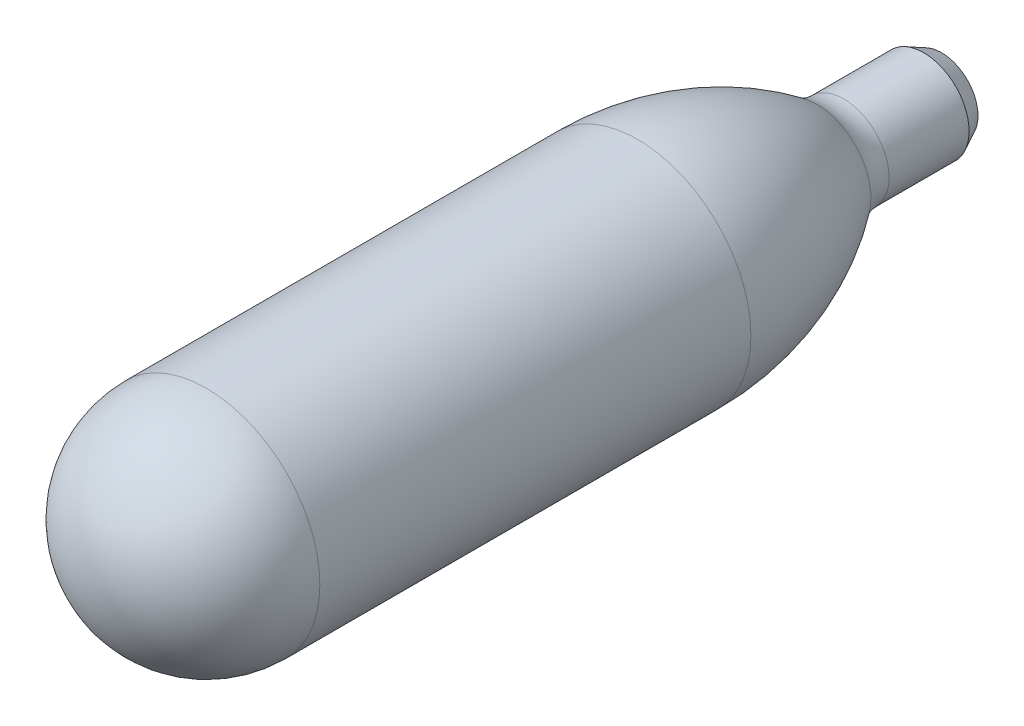
SolidWorks part; units mm, degrees
material "AISI 304"
ref_plane "Front Plane" through (0, 0, 0) normal (0, 0, 1) x (1, 0, 0)
ref_plane "Top Plane" through (0, 0, 0) normal (0, 1, 0) x (1, 0, 0)
ref_plane "Right Plane" through (0, 0, 0) normal (1, 0, 0) x (0, 0, -1)
sketch "Sketch1" plane through (0, 0, 0) normal (1, 0, 0) x (0, 0, -1)
  line L0 (0, 0) -> (95, 0)
  line L1 (95, 0) -> (95, 5.08)
  line L2 (95, 5.08) -> (84.0428, 5.08)
  line L3 (12.7, 12.7) -> (60.96, 12.7)
  line L4 (0, 0) -> (76.6872, 0) construction
  arc A0 (0, 0) -> (12.7, 12.7) centre (12.7, 0) cw
  arc A1 (60.96, 12.7) -> (81.0184, 6.0784) centre (60.96, -20.9916) cw
  arc A2 (84.0428, 5.08) -> (81.0184, 6.0784) centre (84.0428, 10.16) cw
  point P11 (82.3, 5.08)
  dimension "D4" = 12.7
  dimension "D6" = 5.08
  dimension "D1" = 95
  dimension "D2" = 5.08
  dimension "D3" = 12.7
  dimension "D5" = 48.26
revolve "Revolve1" add sketch "Sketch1" angle 360 about L4
chamfer "Chamfer1" distance 1 distance2 2 1 edges at (5.08, 0, -95)
shell "Shell1" thickness 1.25
sketch "Sketch3" plane through (0, 0, -95) normal (0, 0, -1) x (-1, 0, 0)
  circle A0 centre (0, 0) radius 3.318
  circle A2 centre (0, 0) radius 4.08 construction
  dimension "D1" = 0.762
extrude "Cut-Extrude1" cut sketch "Sketch3" against normal blind 2.54
